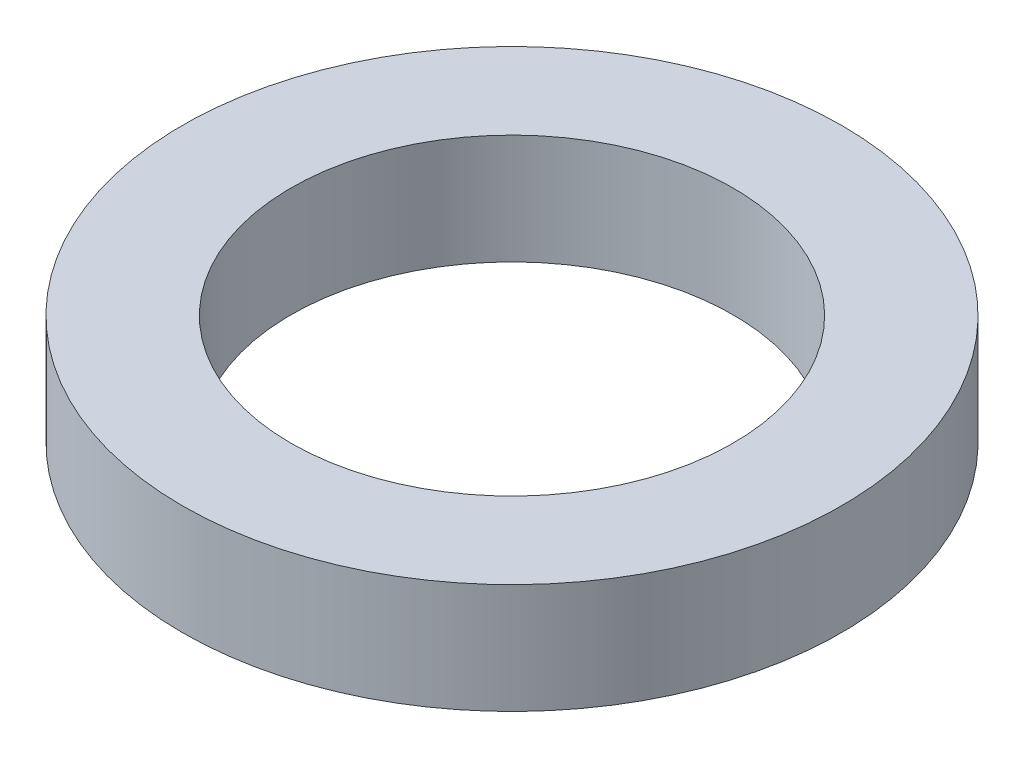
SolidWorks part; units mm, degrees
ref_plane "Front Plane" through (0, 0, 0) normal (0, 0, 1) x (1, 0, 0)
ref_plane "Top Plane" through (0, 0, 0) normal (0, 1, 0) x (1, 0, 0)
ref_plane "Right Plane" through (0, 0, 0) normal (1, 0, 0) x (0, 0, -1)
sketch "Sketch1" plane through (0, 0, 0) normal (0, 1, 0) x (1, 0, 0)
  circle A0 centre (0, 0) radius 4.025
  circle A1 centre (0, 0) radius 6
  dimension "D1" = 8.05
  dimension "D2" = 12
extrude "Boss-Extrude1" add sketch "Sketch1" along normal blind 2
